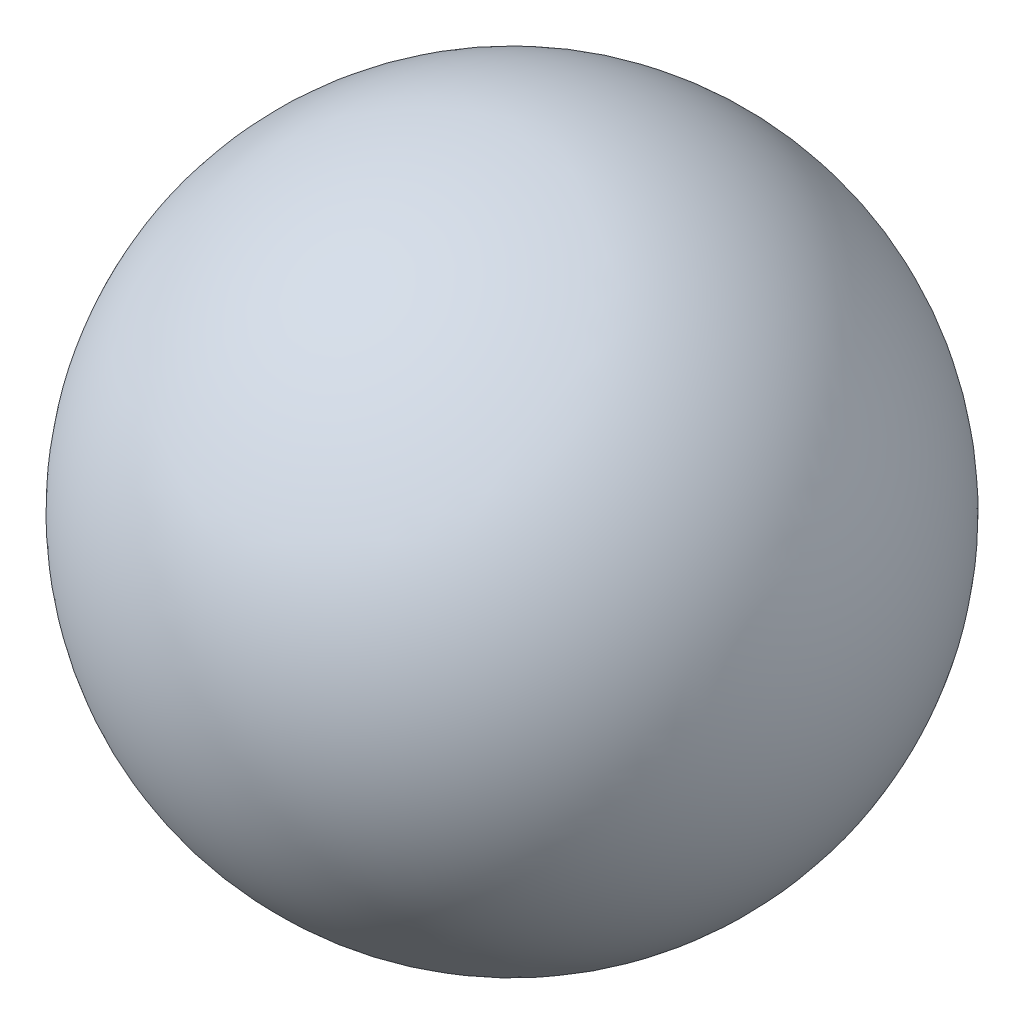
SolidWorks part; units mm, degrees
ref_plane "Front Plane" through (0, 0, 0) normal (0, 0, 1) x (1, 0, 0)
ref_plane "Top Plane" through (0, 0, 0) normal (0, 1, 0) x (1, 0, 0)
ref_plane "Right Plane" through (0, 0, 0) normal (1, 0, 0) x (0, 0, -1)
sketch "Sketch1" plane through (0, 0, 0) normal (0, 1, 0) x (1, 0, 0)
  line L0 (-8, 0) -> (8, 0)
  arc A0 (-8, 0) -> (8, 0) centre (0, 0) ccw
revolve "Revolve1" add sketch "Sketch1" angle 360 about L0
